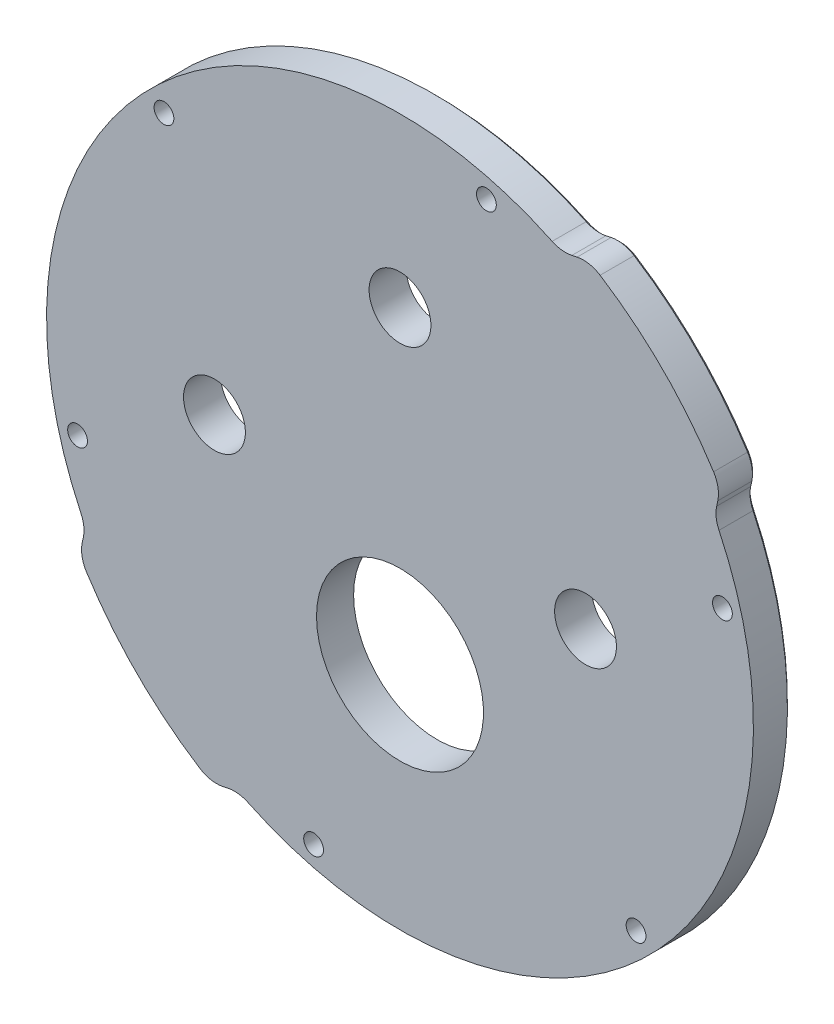
SolidWorks part; units mm, degrees
ref_plane "前视基准面" through (0, 0, 0) normal (0, 0, 1) x (1, 0, 0)
ref_plane "上视基准面" through (0, 0, 0) normal (0, 1, 0) x (1, 0, 0)
ref_plane "右视基准面" through (0, 0, 0) normal (1, 0, 0) x (0, 0, -1)
ref_plane "基准面4" through (0, 0, 6) normal (0, 0, 1) x (1, 0, 0)
sketch "草图1" plane through (0, 0, 6) normal (0, 0, 1) x (1, 0, 0)
  line L0 (-50.8443, -26.0956) -> (-51.7953, -30.5821)
  line L1 (30.5821, 51.7953) -> (26.0956, 50.8443)
  arc A0 (-51.7953, -30.5821) -> (30.5821, 51.7953) centre (0, 0) ccw
  arc A1 (26.0956, 50.8443) -> (-50.8443, -26.0956) centre (0, 0) ccw
extrude "凸台-拉伸1" add sketch "草图1" against normal blind 6
sketch "草图2" plane through (0, 0, 0) normal (0, 0, -1) x (-1, 0, 0)
  line L0 (30.5821, -51.7953) -> (26.0956, -50.8443)
  line L1 (-50.8443, 26.0956) -> (-51.7953, 30.5821)
  arc A0 (26.0956, -50.8443) -> (-50.8443, 26.0956) centre (0, 0) cw
  arc A1 (-51.7953, 30.5821) -> (30.5821, -51.7953) centre (0, 0) ccw
extrude "切除-拉伸1" cut sketch "草图2" against normal through all
hole_wizard "M24 间隙孔1" positions "草图4" profile "草图3" hole size "M24" standard "ANSI Metric"
sketch "草图4" plane through (0, 0, 0) normal (0, 0, -1) x (-1, 0, 0)
  point P0 (0, -20)
sketch "草图3" plane through (0, -20, 0) normal (1, 0, 0) x (0, 1, 0)
  line L0 (0, 0) -> (0, 6)
  line L1 (0, 6) -> (13.5, 6)
  line L2 (13.5, 6) -> (13.5, 0)
  line L5 (13.5, 0) -> (0, 0)
  line L11 (0, -6.35) -> (0, 107.95) construction
  dimension "通孔孔直径" = 27
  dimension "通孔孔深度" = 6
hole_wizard "Ø10.0 (10) 直径孔1" positions "草图6" profile "草图5" hole size "Ø10.0" standard "ANSI Metric"
sketch "草图6" plane through (0, 0, 0) normal (0, 0, -1) x (-1, 0, 0)
  point P0 (0, 30)
  point P1 (-30, 0)
  point P2 (30, 0)
sketch "草图5" plane through (0, 30, 0) normal (1, 0, 0) x (0, 1, 0)
  line L0 (0, 0) -> (0, 6)
  line L1 (0, 6) -> (5, 6)
  line L2 (5, 6) -> (5, 0)
  line L5 (5, 0) -> (0, 0)
  line L11 (0, -6.35) -> (0, 107.95) construction
  dimension "通孔孔直径" = 10
  dimension "通孔孔深度" = 6
hole_wizard "Ø3.2 (3.2) 直径孔1" positions "草图8" profile "草图7" hole size "Ø3.2" standard "ANSI Metric"
sketch "草图8" plane through (0, 0, 0) normal (0, 0, -1) x (-1, 0, 0)
  point P0 (38.1661, 38.1661)
  point P1 (13.9698, -52.1358)
  point P2 (-13.9698, 52.1358)
  point P3 (-52.1358, 13.9698)
  point P4 (-38.1661, -38.1661)
  point P5 (52.1358, -13.9698)
sketch "草图7" plane through (-38.1661, 38.1661, 0) normal (1, 0, 0) x (0, 1, 0)
  line L0 (0, 0) -> (0, 6)
  line L1 (0, 6) -> (1.6, 6)
  line L2 (1.6, 6) -> (1.6, 0)
  line L5 (1.6, 0) -> (0, 0)
  line L11 (0, -6.35) -> (0, 107.95) construction
  dimension "通孔孔直径" = 3.2
  dimension "通孔孔深度" = 6
fillet "圆角1" radius 5 8 edges at (-26.0956, -50.8443, 3) (30.5821, 51.7953, 3) (50.8443, 26.0956, 3) (-30.5821, -51.7953, 3) (26.0956, 50.8443, 3) (-50.8443, -26.0956, 3) (51.7953, 30.5821, 3) (-51.7953, -30.5821, 3)
chamfer "倒角1" distance 0.5 angle 45 16 edges at (-40.4112, 40.4112, 0) (26.1675, 51.1303, 0) (-51.1303, -26.1675, 0) (28.2121, 51.293, 0) (-51.293, -28.2121, 0) (30.5606, 51.41, 0) (-51.41, -30.5606, 0) (42.5325, 42.5325, 0) (-42.5325, -42.5325, 0) (51.41, 30.5606, 0) (-30.5606, -51.41, 0) (51.293, 28.2121, 0) (-28.2121, -51.293, 0) (51.1303, 26.1675, 0) (-26.1675, -51.1303, 0) (40.4112, -40.4112, 0)
